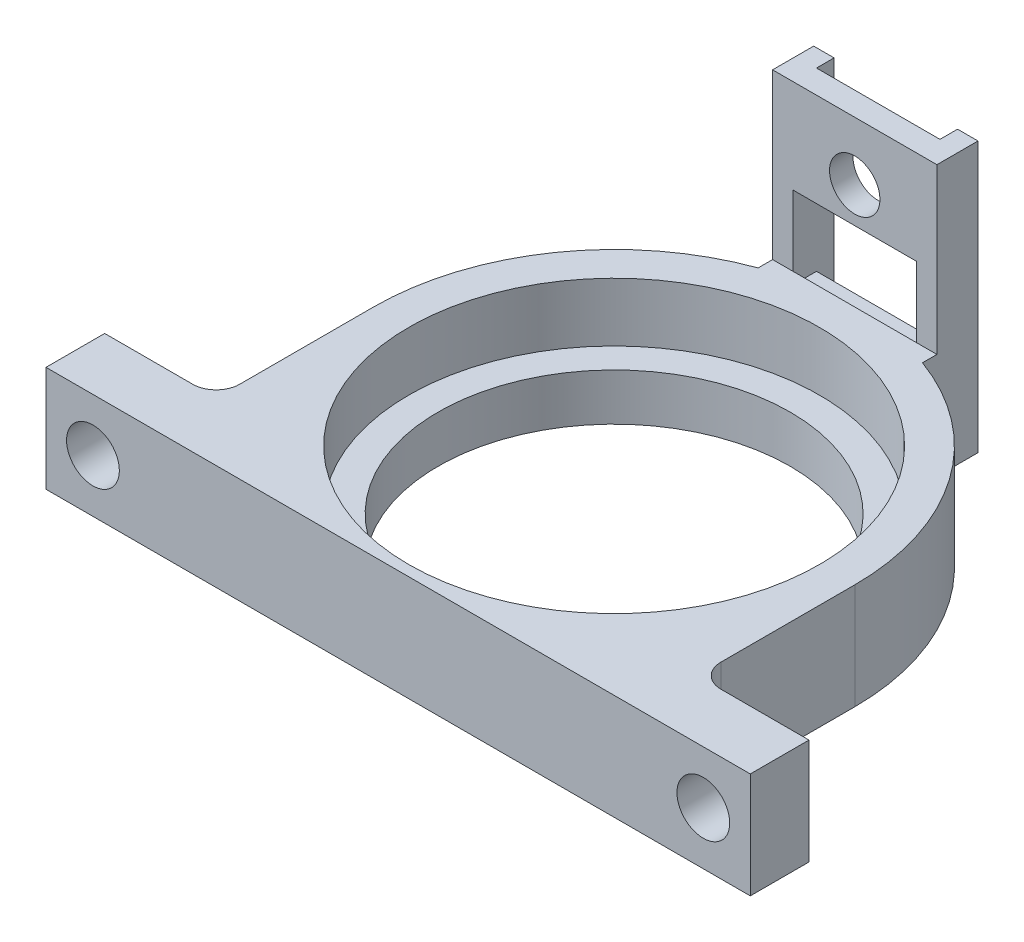
SolidWorks part; units mm, degrees
ref_plane "Front Plane" through (0, 0, 0) normal (0, 0, 1) x (1, 0, 0)
ref_plane "Top Plane" through (0, 0, 0) normal (0, 1, 0) x (1, 0, 0)
ref_plane "Right Plane" through (0, 0, 0) normal (1, 0, 0) x (0, 0, -1)
sketch "Sketch1" plane through (0, 0, 0) normal (0, 1, 0) x (1, 0, 0)
  line L0 (0, 0) -> (0, 38.9) construction
  line L1 (-30, 0) -> (30, 0) construction
  line L3 (0, 0) -> (30, 0)
  line L4 (30, 0) -> (30, 5)
  line L6 (20.5, 18.4) -> (20.5, 5)
  line L7 (20.5, 5) -> (30, 5)
  line L8 (-20.5, 5) -> (-30, 5)
  line L9 (-20.5, 18.4) -> (-20.5, 5)
  line L10 (-30, 0) -> (-30, 5)
  line L11 (0, 0) -> (-30, 0)
  arc A1 (-20.5, 18.4) -> (20.5, 18.4) centre (0, 18.4) cw
  circle A2 centre (0, 18.4) radius 17.5
  dimension "D1" = 35
  dimension "D3" = 3
  dimension "D2" = 18.4
  dimension "D4" = 5
  dimension "D5" = 30
extrude "Boss-Extrude1" add sketch "Sketch1" along normal blind 5 contours A1 L9 L8 L10 L11 L3 L4 L7 L6 A2
sketch "Sketch3" plane through (0, 0, 0) normal (0, -1, 0) x (1, 0, 0)
  line L12 (20.5, -18.4) -> (20.5, -5) construction
  line L17 (20.5, -5) -> (30, -5) construction
  line L18 (30, 0) -> (30, -5) construction
  line L19 (30, 0) -> (-30, 0) construction
  line L20 (-30, 0) -> (-30, -5) construction
  line L21 (-20.5, -5) -> (-30, -5) construction
  line L22 (-20.5, -18.4) -> (-20.5, -5) construction
  line L23 (20.5, -18.4) -> (20.5, -5)
  line L24 (20.5, -5) -> (30, -5)
  line L25 (30, 0) -> (30, -5)
  line L26 (30, 0) -> (-30, 0)
  line L27 (-30, 0) -> (-30, -5)
  line L28 (-20.5, -5) -> (-30, -5)
  line L29 (-20.5, -18.4) -> (-20.5, -5)
  arc A8 (-20.5, -18.4) -> (20.5, -18.4) centre (0, -18.4) ccw construction
  arc A9 (-20.5, -18.4) -> (20.5, -18.4) centre (0, -18.4) ccw
  circle A10 centre (0, -18.4) radius 15
  dimension "D1" = 30
extrude "Boss-Extrude2" add sketch "Sketch3" along normal blind 4
fillet "Fillet2" radius 2 2 edges at (-20.5, 0.5, -5) (20.5, 0.5, -5)
hole_wizard "#8 Clearance Hole1" positions "Sketch4" profile "Sketch5" hole size "#8" standard "ANSI Inch"
sketch "Sketch4" plane through (0, 0, -5) normal (0, 0, -1) x (-1, 0, 0)
  line L0 (-30, 0.5) -> (30, 0.5) construction
  line L1 (-30, 5) -> (-30, -4) construction
  line L2 (30, 5) -> (30, -4) construction
  line L3 (0, 0.5) -> (0, 5) construction
  line L6 (20.5, 5) -> (-20.5, 5) construction
  point P0 (-26, 0.5)
  point P2 (26, 0.5)
  dimension "D1" = 52
sketch "Sketch5" plane through (26, 0.5, -5) normal (1, 0, 0) x (0, 1, 0)
  line L0 (0, 0) -> (0, 25.1007)
  line L1 (0, 25.1007) -> (2.2479, 23.75)
  line L2 (2.2479, 23.75) -> (2.2479, 0)
  line L5 (2.2479, 0) -> (0, 0)
  line L10 (0, 25.1007) -> (-2.2479, 23.75) construction
  line L11 (0, -6.35) -> (0, 107.95) construction
  dimension "Hole Dia." = 4.4958
  dimension "Hole Depth" = 23.75
  dimension "Drill Angle" = 118
sketch "Sketch6" plane through (0, -4, 0) normal (0, -1, 0) x (1, 0, 0)
  line L0 (7, -37.6678) -> (7, -42.4)
  line L1 (7, -42.4) -> (5.26, -42.4)
  line L4 (5.26, -42.4) -> (5.26, -40.9)
  line L5 (5.26, -40.9) -> (-5.26, -40.9)
  line L6 (-5.26, -40.9) -> (-5.26, -42.4)
  line L9 (-5.26, -42.4) -> (-7, -42.4)
  line L10 (-7, -42.4) -> (-7, -37.6678)
  line L11 (0, -18.4) -> (0, -40.9) construction
  arc A0 (7, -37.6678) -> (-7, -37.6678) centre (0, -18.4) cw
  arc A1 (-20.5, -18.4) -> (20.5, -18.4) centre (0, -18.4) ccw construction
  point P9 (-10.444, -54.2285)
  point P10 (0, 0)
  point P14 (10.3232, -54.2285)
  point P15 (0, 0)
  point P16 (0, -49.469)
  point P19 (0, 0)
  point P20 (0, 0)
  point P21 (0, 0)
  point P22 (7, -40.0339)
  point P23 (0, -38.9)
  point P24 (0, 0)
  dimension "D1" = 14
  dimension "D2" = 10.52
  dimension "D3" = 2
  dimension "D4" = 1.5
extrude "Boss-Extrude3" add sketch "Sketch6" against normal up to surface (9 mm away) up to face at (0, 5, -0.9)
sketch "Sketch7" plane through (0, 5, 0) normal (0, 1, 0) x (1, 0, 0)
  line L0 (-5.26, 42.4) -> (-5.26, 40.9) construction
  line L1 (-5.26, 40.9) -> (5.26, 40.9) construction
  line L2 (5.26, 42.4) -> (7, 42.4) construction
  line L3 (5.26, 40.9) -> (5.26, 42.4) construction
  line L6 (-7, 42.4) -> (-5.26, 42.4) construction
  line L7 (5.26, 42.4) -> (7, 42.4)
  line L8 (5.26, 40.9) -> (5.26, 42.4)
  line L9 (-7, 42.4) -> (-7, 38.9)
  line L10 (-7, 38.9) -> (7, 38.9)
  line L11 (-7, 42.4) -> (-5.26, 42.4)
  line L12 (-5.26, 42.4) -> (-5.26, 40.9)
  line L13 (-5.26, 40.9) -> (5.26, 40.9)
  line L14 (7, 42.4) -> (7, 37.6678) construction
  line L15 (7, 38.9) -> (7, 42.4)
  arc A0 (-7, 37.6678) -> (-20.5, 18.4) centre (0, 18.4) ccw construction
extrude "Boss-Extrude4" add sketch "Sketch7" along normal blind 14
sketch "Sketch8" plane through (0, 0, -40.9) normal (0, 0, -1) x (-1, 0, 0)
  line L0 (7, 5) -> (-7, 5) construction
  line L1 (7, 5) -> (-7, 5) construction
  line L2 (0, 0) -> (0, 14) construction
  circle A0 centre (0, 14) radius 2.1463
  dimension "D2" = 4.2926
  dimension "D1" = 9
extrude "Cut-Extrude1" cut sketch "Sketch8" against normal through all
sketch "Sketch9" plane through (0, 0, -40.9) normal (0, 0, -1) x (-1, 0, 0)
  line L0 (-5.26, 19) -> (-5.26, -4) construction
  line L1 (-5.26, 4) -> (5.26, 4)
  line L2 (-5.26, 4) -> (-5.26, 11)
  line L3 (-5.26, 11) -> (5.26, 11)
  line L4 (5.26, 4) -> (5.26, 11)
  line L5 (-5.26, 4) -> (5.26, 11) construction
  line L6 (-5.26, 11) -> (5.26, 4) construction
  line L7 (5.26, 19) -> (5.26, -4) construction
  line L8 (5.26, -4) -> (-5.26, -4) construction
  circle A0 centre (0, 14) radius 2.1463 construction
  point P4 (0, 7.5)
  dimension "D1" = 8
  dimension "D2" = 3
extrude "Cut-Extrude2" cut sketch "Sketch9" against normal up to surface (2 mm away) up to face at (-2.1463, 14, -38.9)
